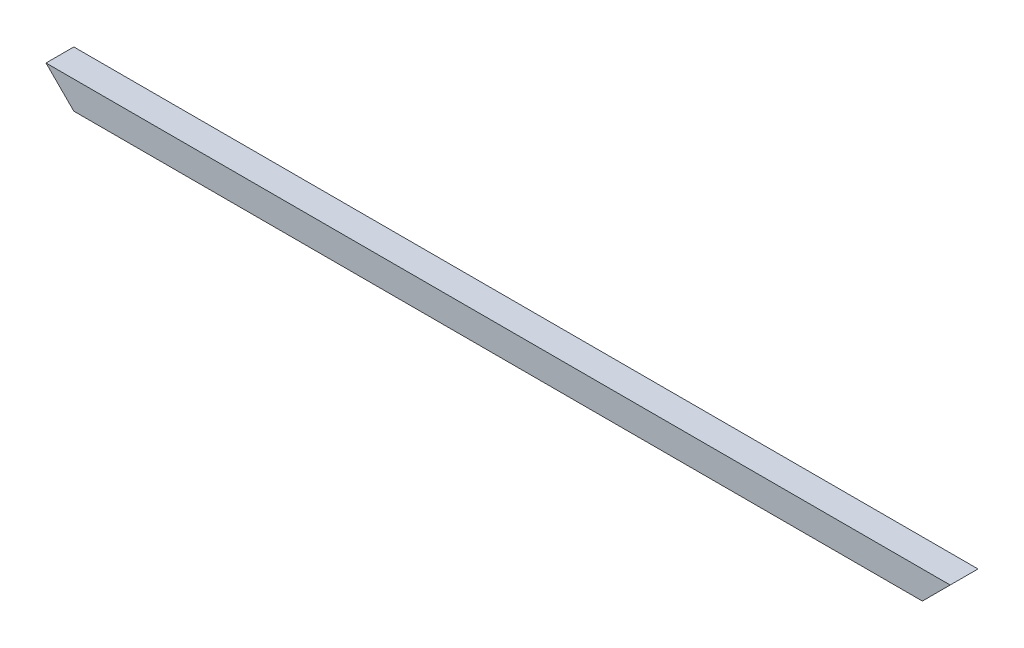
SolidWorks part; units mm, degrees
material "Stainless Steel (ferritic)"
ref_plane "Front Plane" through (0, 0, 0) normal (0, 0, 1) x (1, 0, 0)
ref_plane "Top Plane" through (0, 0, 0) normal (0, 1, 0) x (1, 0, 0)
ref_plane "Right Plane" through (0, 0, 0) normal (1, 0, 0) x (0, 0, -1)
sketch "Sketch1" plane through (0, 0, 0) normal (1, 0, 0) x (0, 0, -1)
  line L0 (-8.8, 8.8) -> (8.8, 8.8)
  line L1 (-10, -10) -> (10, -10)
  line L2 (-10, -10) -> (-10, 10)
  line L3 (-10, 10) -> (10, 10)
  line L4 (10, -10) -> (10, 10)
  line L5 (-10, -10) -> (10, 10) construction
  line L6 (-10, 10) -> (10, -10) construction
  line L7 (8.8, -8.8) -> (8.8, 8.8)
  line L8 (-8.8, -8.8) -> (8.8, -8.8)
  line L9 (-8.8, -8.8) -> (-8.8, 8.8)
  point P0 (0, 0)
  dimension "D1" = 20
  dimension "D2" = 20
  dimension "D3" = 1.2
extrude "Boss-Extrude1" add sketch "Sketch1" along normal blind 650
sketch "Sketch2" plane through (0, 0, -10) normal (0, 0, -1) x (-1, 0, 0)
  line L0 (0, 10) -> (-20, -10)
  line L1 (-650, -10) -> (0, -10) construction
  line L2 (0, -10) -> (0, 10) construction
  dimension "D1" = 45
extrude "Cut-Extrude1" cut sketch "Sketch2" against normal through all and the other way through all
sketch "Sketch3" plane through (0, 0, -10) normal (0, 0, -1) x (-1, 0, 0)
  line L0 (-650, 10) -> (-630, -10)
  line L1 (-650, -10) -> (-20, -10) construction
  line L2 (-650, -10) -> (-650, 10) construction
  dimension "D1" = 45
extrude "Cut-Extrude3" cut sketch "Sketch3" against normal through all and the other way through all flip side to cut
